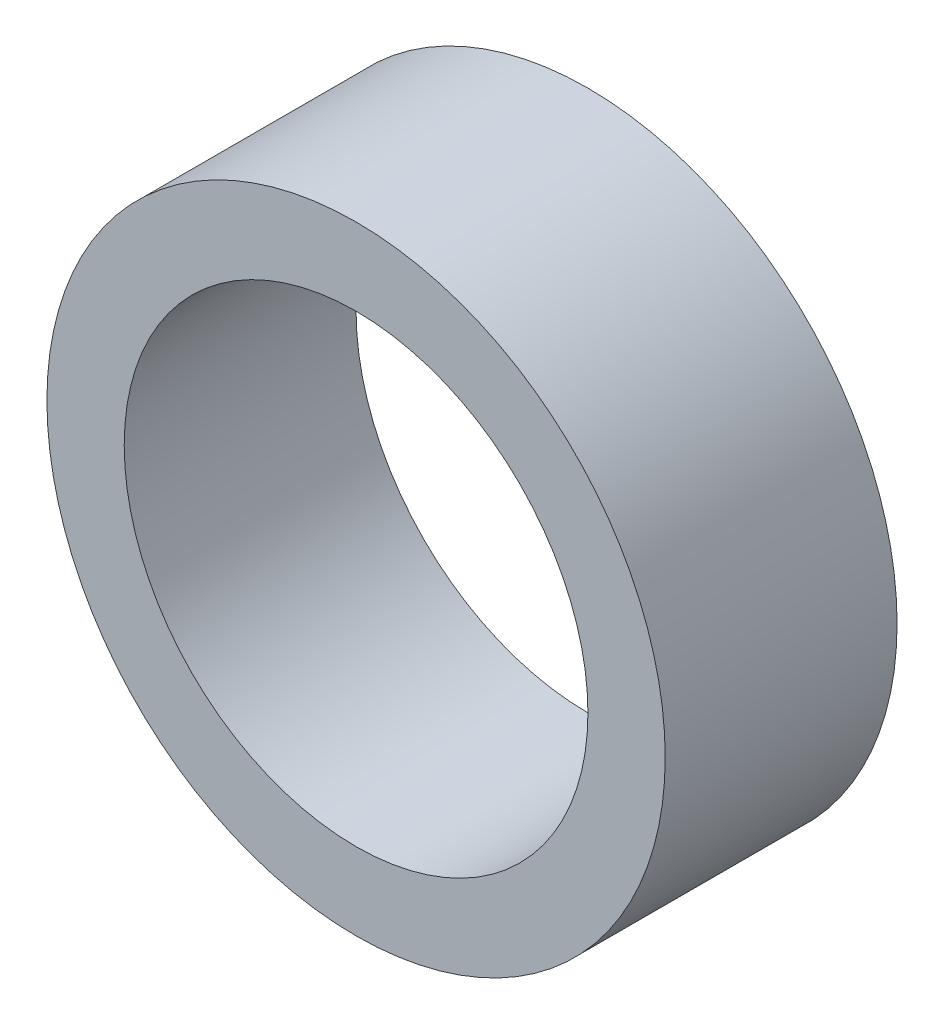
SolidWorks part; units mm, degrees
material "Phosphor bronze 10% D, UNS C52400"
ref_plane "Front Plane" through (0, 0, 0) normal (0, 0, 1) x (1, 0, 0)
ref_plane "Top Plane" through (0, 0, 0) normal (0, 1, 0) x (1, 0, 0)
ref_plane "Right Plane" through (0, 0, 0) normal (1, 0, 0) x (0, 0, -1)
sketch "Sketch1" plane through (0, 0, 0) normal (0, 0, 1) x (1, 0, 0)
  circle A0 centre (0, 0) radius 9.525
  circle A1 centre (0, 0) radius 12.7
  dimension "D1" = 19.05
  dimension "D2" = 25.4
extrude "Boss-Extrude1" add sketch "Sketch1" along normal blind 9.525
